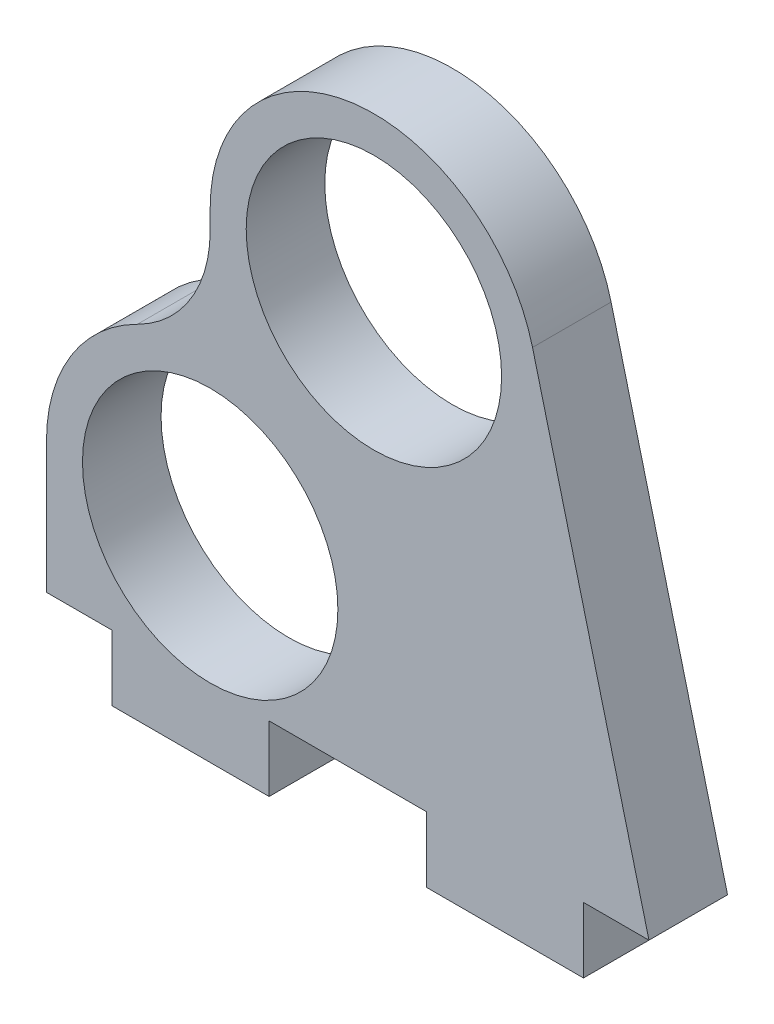
SolidWorks part; units mm, degrees
ref_plane "Alzado" through (0, 0, 0) normal (0, 0, 1) x (1, 0, 0)
ref_plane "Planta" through (0, 0, 0) normal (0, 1, 0) x (1, 0, 0)
ref_plane "Vista lateral" through (0, 0, 0) normal (1, 0, 0) x (0, 0, -1)
sketch "Croquis1" plane through (0, 0, 0) normal (0, 0, 1) x (1, 0, 0)
  line L0 (-12.5, 0) -> (-12.5, -10)
  line L1 (0, 0) -> (12.5, 21.6506) construction
  line L3 (-12.5, -10) -> (-7.5, -10) construction
  line L5 (4.5, -15) -> (-7.5, -15)
  line L6 (28.5, -15) -> (16.5, -15)
  line L9 (-12.5, -10) -> (-7.5, -10)
  line L10 (-7.5, -15) -> (-7.5, -10)
  line L14 (28.5, -15) -> (28.5, -10)
  line L16 (16.5, -15) -> (16.5, -10)
  line L17 (16.5, -10) -> (4.5, -10)
  line L18 (4.5, -15) -> (4.5, -10)
  line L19 (12.5, 21.6506) -> (0, 21.6506) construction
  line L20 (0, 21.6506) -> (0, 20.1556)
  line L21 (28.5, -10) -> (33.5, -10)
  line L23 (4.5, -10) -> (16.5, -10) construction
  line L24 (33.5, -10) -> (24.61, 24.7488)
  arc A0 (-5.5556, 11.1976) -> (-12.5, 0) centre (0, 0) ccw
  circle A1 centre (0, 0) radius 9.75
  arc A2 (24.61, 24.7488) -> (0, 21.6506) centre (12.5, 21.6506) ccw
  circle A3 centre (12.5, 21.6506) radius 9.75
  arc A5 (0, 20.1556) -> (-5.5556, 11.1976) centre (-10, 20.1556) cw
  point P14 (0, 12.5)
  dimension "D1" = 19.5
  dimension "D2" = 25
  dimension "D4" = 19.5
  dimension "D5" = 25
  dimension "D8" = 10
  dimension "D3" = 25
  dimension "D6" = 10
  dimension "D7" = 60
  dimension "D9" = 5
  dimension "D10" = 5
  dimension "D11" = 12
  dimension "D12" = 12
  dimension "D13" = 12
  dimension "D14" = 5
extrude "Saliente-Extruir1" add sketch "Croquis1" along normal blind 6
